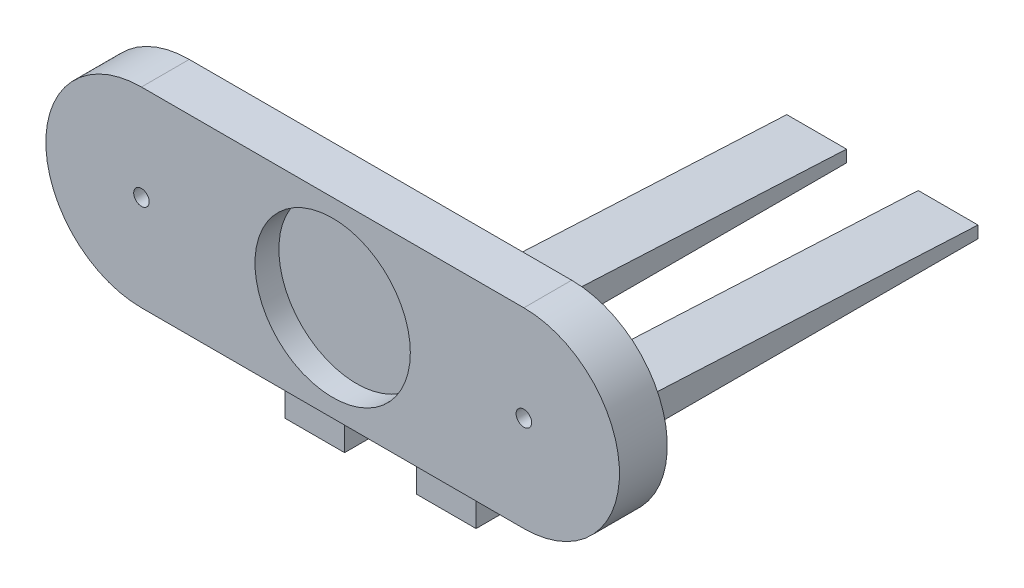
SolidWorks part; units mm, degrees
ref_plane "정면" through (0, 0, 0) normal (0, 0, 1) x (1, 0, 0)
ref_plane "윗면" through (0, 0, 0) normal (0, 1, 0) x (1, 0, 0)
ref_plane "우측면" through (0, 0, 0) normal (1, 0, 0) x (0, 0, -1)
sketch "스케치3" plane through (0, 0, 0) normal (0, 0, 1) x (1, 0, 0)
  line L0 (-80, 0) -> (80, 0) construction
  line L1 (-80, 40) -> (80, 40)
  line L2 (-80, -40) -> (80, -40)
  arc A0 (-80, 40) -> (-80, -40) centre (-80, 0) ccw
  arc A1 (80, -40) -> (80, 40) centre (80, 0) ccw
  point P3 (0, 0)
  dimension "D2" = 80
  dimension "D1" = 160
extrude "보스-돌출1" add sketch "스케치3" against normal blind 20
sketch "스케치4" plane through (0, 0, 0) normal (0, 0, 1) x (1, 0, 0)
  circle A0 centre (0, 0) radius 32.5
  dimension "D1" = 65
extrude "컷-돌출4" cut sketch "스케치4" against normal blind 10
sketch "스케치10" plane through (0, 0, -20) normal (0, 0, -1) x (-1, 0, 0)
  line L1 (-40, 7.5) -> (-15, 7.5)
  line L2 (-40, 7.5) -> (-40, -70)
  line L3 (-40, -70) -> (-15, -70)
  line L4 (-15, 7.5) -> (-15, -70)
  line L5 (15, 7.5) -> (40, 7.5)
  line L6 (15, 7.5) -> (15, -70)
  line L7 (15, -70) -> (40, -70)
  line L8 (40, 7.5) -> (40, -70)
  dimension "D1" = 40
  dimension "D2" = 25
  dimension "D3" = 25
  dimension "D4" = 40
  dimension "D5" = 77.5
  dimension "D6" = 7.5
  dimension "D7" = 77.5
  dimension "D8" = 7.5
extrude "보스-돌출5" add sketch "스케치10" along normal blind 10
sketch "스케치14" plane through (0, 0, -30) normal (0, 0, -1) x (-1, 0, 0)
  line L0 (-15, -70) -> (-15, 7.5) construction
  line L1 (-40, -70) -> (-15, -70)
  line L2 (-40, -70) -> (-40, -55)
  line L3 (-40, -55) -> (-15, -55)
  line L4 (-15, -70) -> (-15, -55)
  line L5 (40, -70) -> (40, 7.5) construction
  line L6 (15, -70) -> (40, -70)
  line L7 (15, -70) -> (15, -55)
  line L8 (15, -55) -> (40, -55)
  line L9 (40, -70) -> (40, -55)
  dimension "D1" = 15
  dimension "D2" = 15
extrude "보스-돌출6" add sketch "스케치14" along normal blind 200
sketch "스케치15" plane through (40, 0, 0) normal (1, 0, 0) x (0, 0, -1)
  line L0 (30, -55) -> (230, -65)
  line L1 (230, -55) -> (230, -70) construction
  line L2 (230, -65) -> (230, -55)
  line L3 (230, -55) -> (30, -55)
  dimension "D1" = 10
extrude "컷-돌출5" cut sketch "스케치15" against normal through all
sketch "스케치16" plane through (0, 0, -20) normal (0, 0, -1) x (-1, 0, 0)
  circle A0 centre (-80, 0) radius 3.25
  circle A1 centre (80, 0) radius 3.25
  dimension "D1" = 6.5
  dimension "D2" = 6.5
extrude "컷-돌출6" cut sketch "스케치16" against normal through all
sketch "스케치17" plane through (0, 0, -20) normal (0, 0, -1) x (-1, 0, 0)
  circle A0 centre (-80, 0) radius 5.75
  circle A1 centre (80, 0) radius 5.75
  dimension "D1" = 11.5
  dimension "D2" = 11.5
extrude "컷-돌출7" cut sketch "스케치17" against normal blind 10
